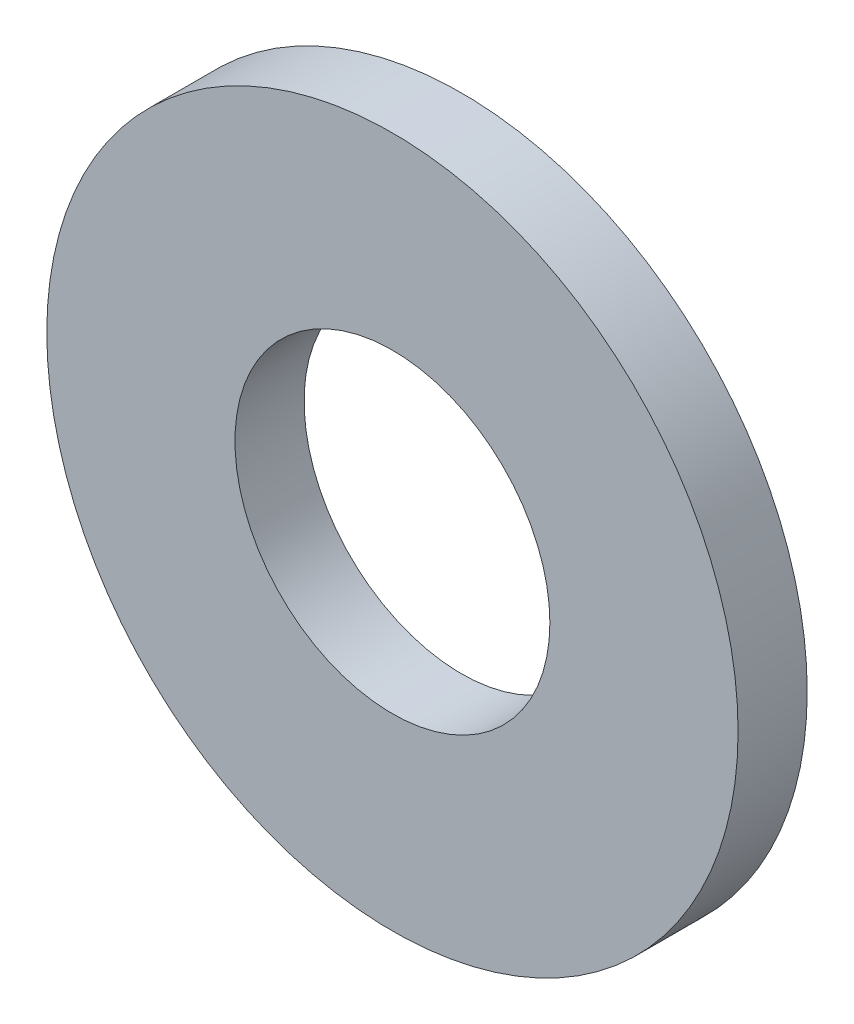
SolidWorks part; units mm, degrees
material "AISI 1020"
ref_plane "Plano frontal" through (0, 0, 0) normal (0, 0, 1) x (1, 0, 0)
ref_plane "Plano superior" through (0, 0, 0) normal (0, 1, 0) x (1, 0, 0)
ref_plane "Plano direito" through (0, 0, 0) normal (1, 0, 0) x (0, 0, -1)
sketch "Esboço1" plane through (0, 0, 0) normal (0, 0, 1) x (1, 0, 0)
  circle A0 centre (0, 0) radius 2.05
  circle A1 centre (0, 0) radius 4.5
  dimension "D1" = 9
  dimension "D2" = 4.1
extrude "Ressalto-extrusão1" add sketch "Esboço1" along normal blind 0.9
